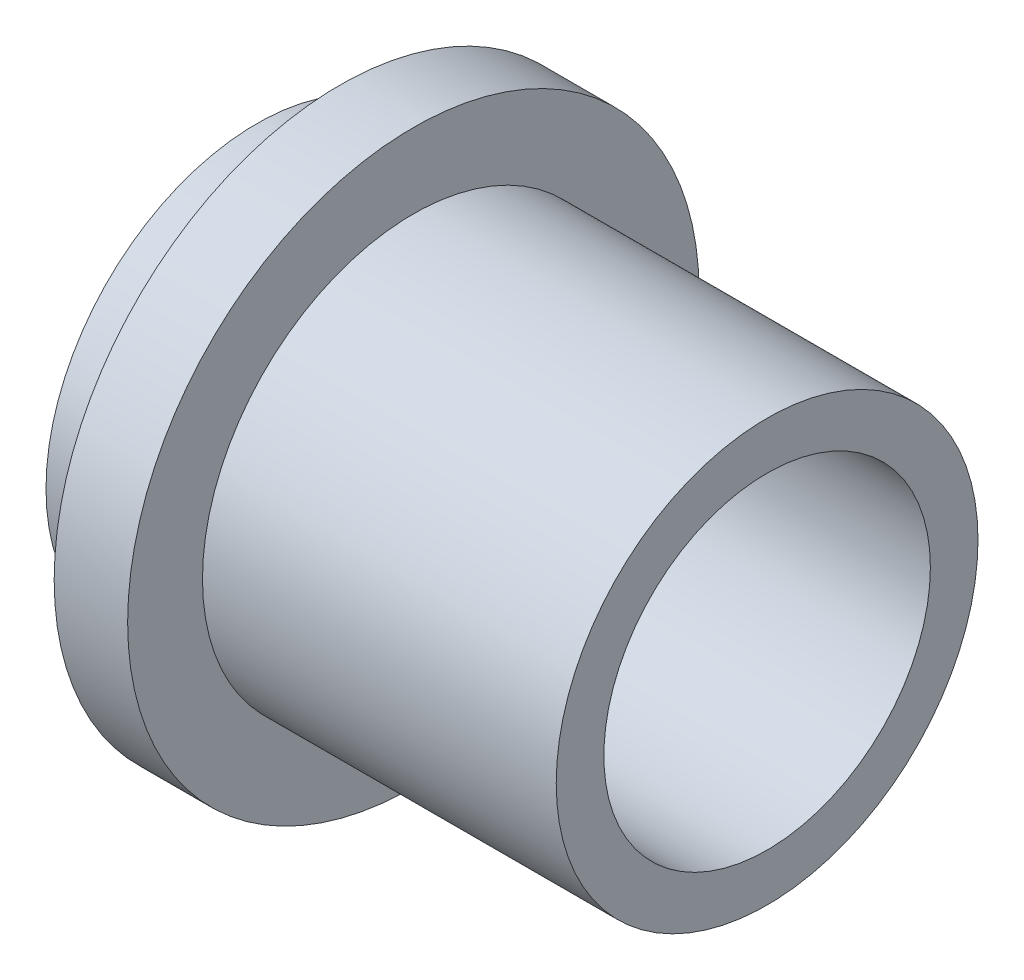
SolidWorks part; units mm, degrees
material "PE Low/Medium Density"
ref_plane "Front Plane" through (0, 0, 0) normal (0, 0, 1) x (1, 0, 0)
ref_plane "Top Plane" through (0, 0, 0) normal (0, 1, 0) x (1, 0, 0)
ref_plane "Right Plane" through (0, 0, 0) normal (1, 0, 0) x (0, 0, -1)
sketch "Sketch1" plane through (0, 0, 0) normal (0, 0, 1) x (1, 0, 0)
  line L0 (-1.9879, 0) -> (8.4749, 0) construction
  line L1 (0, 0) -> (0, 3.937)
  line L2 (0, 3.937) -> (0.635, 3.937)
  line L3 (0.635, 3.937) -> (1.5494, 4.8514)
  line L4 (1.5494, 4.8514) -> (1.5494, 5.334)
  line L5 (1.5494, 5.334) -> (2.921, 5.334)
  line L6 (2.921, 5.334) -> (2.921, 3.937)
  line L7 (2.921, 3.937) -> (9.525, 3.937)
  line L8 (9.525, 3.937) -> (9.525, 0)
  line L9 (9.525, 0) -> (0, 0)
  dimension "D1" = 7.874
  dimension "D2" = 10.668
  dimension "D3" = 9.525
  dimension "D4" = 6.604
  dimension "D5" = 1.3716
  dimension "D6" = 7.874
  dimension "D7" = 0.635
  dimension "D8" = 45
revolve "Revolve1" add sketch "Sketch1" angle 360 about L0
sketch "Sketch2" plane through (0, 0, 0) normal (-1, 0, 0) x (0, 0, 1)
  circle A0 centre (0, 0) radius 3.175
  circle A1 centre (0, 0) radius 3.937
  circle A2 centre (0, 0) radius 3.937
  dimension "D1" = 0
  dimension "D2" = 0.762
hole_wizard "1/4 (0.24) Diameter Hole1" positions "Sketch3" profile "Sketch4" hole size "1/4" standard "ANSI Inch" end condition through all
sketch "Sketch3" plane through (9.525, 0, 0) normal (1, 0, 0) x (0, 0, -1)
  point P0 (0, 0)
sketch "Sketch4" plane through (9.525, 0, 0) normal (0, 1, 0) x (0, 0, -1)
  line L0 (0, 0) -> (0, 9.525)
  line L1 (0, 9.525) -> (3.048, 9.525)
  line L2 (3.048, 9.525) -> (3.048, 0)
  line L5 (3.048, 0) -> (0, 0)
  line L11 (0, -6.35) -> (0, 107.95) construction
  dimension "Thru Hole Dia." = 6.096
  dimension "Thru Hole Depth" = 9.525
